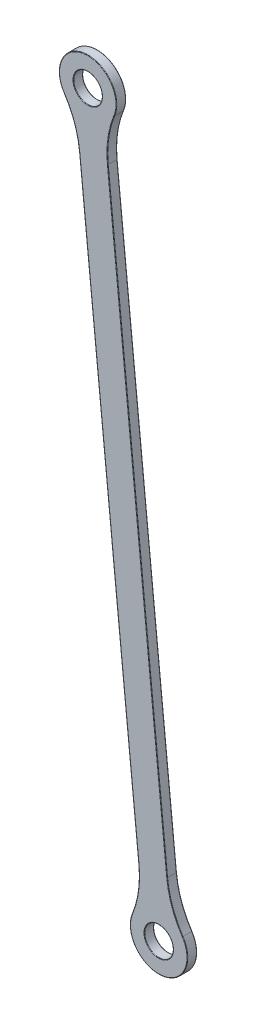
SolidWorks part; units mm, degrees
ref_plane "Front Plane" through (0, 0, 0) normal (0, 0, 1) x (1, 0, 0)
ref_plane "Top Plane" through (0, 0, 0) normal (0, 1, 0) x (1, 0, 0)
ref_plane "Right Plane" through (0, 0, 0) normal (1, 0, 0) x (0, 0, -1)
sketch "Sketch1" plane through (0, 0, 0) normal (0, 0, 1) x (1, 0, 0)
  line L0 (14.5, 81.5) -> (-7.7952, 302.3776) construction
  line L1 (14.5, 81.5) -> (-7.7952, 302.3776) construction
  line L2 (-7.7952, 302.3776) -> (14.5, 81.5) construction
  line L3 (-3.3179, 302.8296) -> (18.9772, 81.9519)
  line L4 (-12.2724, 301.9257) -> (10.0228, 81.0481)
  circle A0 centre (-7.7952, 302.3776) radius 9 construction
  circle A1 centre (14.5, 81.5) radius 9 construction
  arc A2 (-3.3179, 302.8296) -> (-12.2724, 301.9257) centre (-7.7952, 302.3776) ccw
  arc A3 (10.0228, 81.0481) -> (18.9772, 81.9519) centre (14.5, 81.5) ccw
  arc A4 (18.9772, 81.9519) -> (10.0228, 81.0481) centre (14.5, 81.5) ccw
  arc A5 (-3.3179, 302.8296) -> (-12.2724, 301.9257) centre (-7.7952, 302.3776) cw
  arc A6 (18.1945, 89.7068) -> (9.24, 88.8029) centre (14.5, 81.5) cw
  arc A7 (-2.5352, 295.0747) -> (-11.4897, 294.1709) centre (-7.7952, 302.3776) ccw
  point P4 (3.3524, 191.9388)
  point P21 (0, 0)
  point P22 (0, 0)
  point P23 (0, 0)
  point P24 (0, 0)
  dimension "D1" = 18
  dimension "D2" = 9
extrude "Boss-Extrude1" add sketch "Sketch1" against normal blind 3 contours A6 L3 A3 L4 | L3 A5 L4 A4 | L3 A7 L4 A2
fillet "Fillet1" radius 30 4 edges at (9.24, 88.8029, -1.5) (18.1945, 89.7068, -1.5) (-11.4897, 294.1709, -1.5) (-2.5352, 295.0747, -1.5)
fillet "Fillet2" radius 0.15 20 edges at (-3.2952, 302.3776, -3) (-3.2952, 302.3776, 0) (19, 81.5, -3) (19, 81.5, 0) (-12.0434, 290.9122, -3) (-12.0434, 290.9122, 0) (-1.1248, 191.4869, -3) (-1.1248, 191.4869, 0) (8.0462, 91.8851, -3) (8.0462, 91.8851, 0) (15.4039, 72.5455, 0) (15.4039, 72.5455, -3) (18.7483, 92.9654, -3) (18.7483, 92.9654, 0) (7.8297, 192.3907, 0) (7.8297, 192.3907, -3) (-1.3413, 291.9925, -3) (-1.3413, 291.9925, 0) (-8.699, 311.3321, -3) (-8.699, 311.3321, 0)
